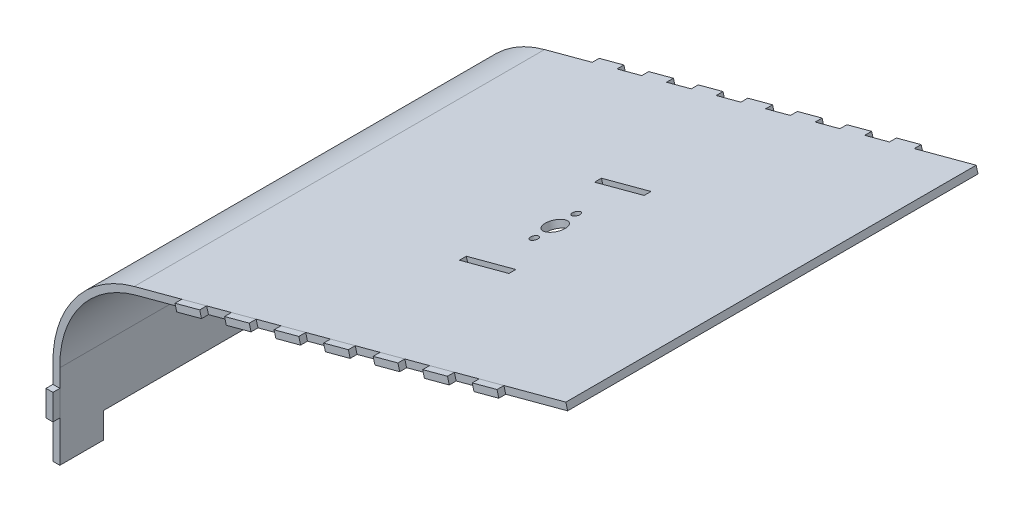
SolidWorks part; units mm, degrees
material "Maple"
ref_plane "Front Plane" through (0, 0, 0) normal (0, 0, 1) x (1, 0, 0)
ref_plane "Top Plane" through (0, 0, 0) normal (0, 1, 0) x (1, 0, 0)
ref_plane "Right Plane" through (0, 0, 0) normal (1, 0, 0) x (0, 0, -1)
sketch "Sketch1" plane through (0, 0, 0) normal (0, 0, 1) x (1, 0, 0)
  line L0 (-100, -27.0742) -> (-100, -60) construction
  line L1 (100, 60) -> (-68.3022, 14.9036) construction
  line L2 (-100, -27.0742) -> (-100, -60)
  line L3 (100, 60) -> (-68.3022, 14.9036)
  arc A0 (-68.3022, 14.9036) -> (-100, -27.0742) centre (-57.2316, -26.4125) ccw construction
  arc A1 (-68.3022, 14.9036) -> (-100, -27.0742) centre (-57.2316, -26.4125) ccw
extrude "Extrude-Thin1" add sketch "Sketch1" against normal blind 160 thin thin type one direction reverse wall 2.7
ref_plane "Plane1" through (0, 0, -80) normal (0, 0, 1) x (1, 0, 0)
sketch "Sketch2" plane through (0, 0, 0) normal (0, 0, 1) x (1, 0, 0)
  line L0 (100, -24) -> (97, -24) construction
  line L1 (97, -14) -> (97, -24) construction
  line L2 (100, -14) -> (97, -14) construction
  line L3 (75.8519, 53.5295) -> (76.6283, 50.6317) construction
  line L4 (-100, -44) -> (-97, -44)
  line L5 (-100, -34) -> (-100, -44)
  line L6 (-97, -34) -> (-100, -34)
  line L7 (-97, -44) -> (-97, -34)
  line L8 (-100, -60) -> (-80, -60)
  line L9 (-80, -60) -> (-80, -50)
  line L10 (-80, -50) -> (80, -50)
  line L11 (80, -50) -> (80, -60)
  line L12 (80, -60) -> (100, -60)
  line L13 (100, -60) -> (100, 60)
  line L14 (100, 60) -> (-68.3022, 14.9036)
  line L15 (-100, -27.0742) -> (-100, -60)
  line L16 (-100, -60) -> (-80, -60)
  line L17 (-80, -60) -> (-80, -50)
  line L18 (-80, -50) -> (80, -50)
  line L19 (80, -50) -> (80, -60)
  line L20 (80, -60) -> (100, -60)
  line L21 (100, -60) -> (100, 60)
  line L22 (100, 60) -> (-68.3022, 14.9036)
  line L23 (-100, -27.0742) -> (-100, -60)
  line L24 (-100, -44) -> (-97, -44)
  line L25 (-100, -34) -> (-100, -44)
  line L26 (-97, -34) -> (-100, -34)
  line L27 (-97, -44) -> (-97, -34)
  line L28 (100, -34) -> (97, -34)
  line L29 (100, -44) -> (100, -34)
  line L30 (97, -44) -> (100, -44)
  line L31 (97, -34) -> (97, -44)
  line L32 (100, -34) -> (97, -34)
  line L33 (100, -44) -> (100, -34)
  line L34 (97, -44) -> (100, -44)
  line L35 (97, -34) -> (97, -44)
  line L36 (-27, -44) -> (-27, -47)
  line L37 (-27, -47) -> (-17, -47)
  line L38 (-17, -47) -> (-17, -44)
  line L39 (-17, -44) -> (-27, -44)
  line L40 (-27, -44) -> (-27, -47)
  line L41 (-27, -47) -> (-17, -47)
  line L42 (-17, -47) -> (-17, -44)
  line L43 (-17, -44) -> (-27, -44)
  line L44 (-47, -44) -> (-47, -47)
  line L45 (-47, -47) -> (-37, -47)
  line L46 (-37, -47) -> (-37, -44)
  line L47 (-37, -44) -> (-47, -44)
  line L48 (-47, -44) -> (-47, -47)
  line L49 (-47, -47) -> (-37, -47)
  line L50 (-37, -47) -> (-37, -44)
  line L51 (-37, -44) -> (-47, -44)
  line L52 (-77, -44) -> (-87, -44)
  line L53 (-87, -44) -> (-87, -47)
  line L54 (-87, -47) -> (-77, -47)
  line L55 (-77, -47) -> (-77, -44)
  line L56 (-77, -44) -> (-87, -44)
  line L57 (-87, -44) -> (-87, -47)
  line L58 (-87, -47) -> (-77, -47)
  line L59 (-77, -47) -> (-77, -44)
  line L60 (-67, -44) -> (-67, -47)
  line L61 (-57, -44) -> (-67, -44)
  line L62 (-57, -47) -> (-57, -44)
  line L63 (-67, -47) -> (-57, -47)
  line L64 (-67, -44) -> (-67, -47)
  line L65 (-57, -44) -> (-67, -44)
  line L66 (-57, -47) -> (-57, -44)
  line L67 (-67, -47) -> (-57, -47)
  line L68 (53, -44) -> (53, -47)
  line L69 (53, -47) -> (63, -47)
  line L70 (63, -47) -> (63, -44)
  line L71 (63, -44) -> (53, -44)
  line L72 (53, -44) -> (53, -47)
  line L73 (53, -47) -> (63, -47)
  line L74 (63, -47) -> (63, -44)
  line L75 (63, -44) -> (53, -44)
  line L76 (33, -44) -> (33, -47)
  line L77 (33, -47) -> (43, -47)
  line L78 (43, -47) -> (43, -44)
  line L79 (43, -44) -> (33, -44)
  line L80 (33, -44) -> (33, -47)
  line L81 (33, -47) -> (43, -47)
  line L82 (43, -47) -> (43, -44)
  line L83 (43, -44) -> (33, -44)
  line L84 (13, -44) -> (13, -47)
  line L85 (13, -47) -> (23, -47)
  line L86 (23, -47) -> (23, -44)
  line L87 (23, -44) -> (13, -44)
  line L88 (13, -44) -> (13, -47)
  line L89 (13, -47) -> (23, -47)
  line L90 (23, -47) -> (23, -44)
  line L91 (23, -44) -> (13, -44)
  line L92 (-7, -44) -> (-7, -47)
  line L93 (3, -44) -> (-7, -44)
  line L94 (3, -47) -> (3, -44)
  line L95 (-7, -47) -> (3, -47)
  line L96 (-7, -44) -> (-7, -47)
  line L97 (3, -44) -> (-7, -44)
  line L98 (3, -47) -> (3, -44)
  line L99 (-7, -47) -> (3, -47)
  line L100 (73, -44) -> (73, -47)
  line L101 (83, -44) -> (73, -44)
  line L102 (83, -47) -> (83, -44)
  line L103 (73, -47) -> (83, -47)
  line L104 (73, -44) -> (73, -47)
  line L105 (83, -44) -> (73, -44)
  line L106 (83, -47) -> (83, -44)
  line L107 (73, -47) -> (83, -47)
  line L108 (76.6283, 50.6317) -> (66.9691, 48.0436) construction
  line L109 (66.9691, 48.0436) -> (66.1926, 50.9413) construction
  line L110 (56.5333, 48.3531) -> (57.3098, 45.4554) construction
  line L111 (57.3098, 45.4554) -> (47.6505, 42.8672) construction
  line L112 (47.6505, 42.8672) -> (46.8741, 45.765) construction
  line L113 (100, 36) -> (97, 36) construction
  line L114 (97, 46) -> (97, 36) construction
  line L115 (100, 46) -> (97, 46) construction
  line L116 (100, 16) -> (97, 16) construction
  line L117 (97, 26) -> (97, 16) construction
  line L118 (100, 26) -> (97, 26) construction
  line L119 (100, -4) -> (97, -4) construction
  line L120 (97, 6) -> (97, -4) construction
  line L121 (100, 6) -> (97, 6) construction
  line L122 (-20.7407, 27.6476) -> (-19.9643, 24.7498) construction
  line L123 (-19.9643, 24.7498) -> (-29.6235, 22.1617) construction
  line L124 (-29.6235, 22.1617) -> (-30.4, 25.0594) construction
  line L125 (-1.4222, 32.824) -> (-0.6458, 29.9262) construction
  line L126 (-0.6458, 29.9262) -> (-10.305, 27.338) construction
  line L127 (-10.305, 27.338) -> (-11.0815, 30.2358) construction
  line L128 (17.8963, 38.0004) -> (18.6728, 35.1026) construction
  line L129 (18.6728, 35.1026) -> (9.0135, 32.5144) construction
  line L130 (9.0135, 32.5144) -> (8.237, 35.4122) construction
  line L131 (37.2148, 43.1768) -> (37.9913, 40.279) construction
  line L132 (37.9913, 40.279) -> (28.332, 37.6908) construction
  line L133 (28.332, 37.6908) -> (27.5556, 40.5886) construction
  line L134 (-40.0592, 22.4712) -> (-39.2828, 19.5735) construction
  line L135 (-39.2828, 19.5735) -> (-48.942, 16.9853) construction
  line L136 (-48.942, 16.9853) -> (-49.7185, 19.883) construction
  line L137 (100, -24) -> (97, -24)
  line L138 (97, -14) -> (97, -24)
  line L139 (100, -14) -> (97, -14)
  line L140 (75.8519, 53.5295) -> (76.6283, 50.6317)
  line L141 (76.6283, 50.6317) -> (66.9691, 48.0436)
  line L142 (66.9691, 48.0436) -> (66.1926, 50.9413)
  line L143 (56.5333, 48.3531) -> (57.3098, 45.4554)
  line L144 (57.3098, 45.4554) -> (47.6505, 42.8672)
  line L145 (47.6505, 42.8672) -> (46.8741, 45.765)
  line L146 (100, 36) -> (97, 36)
  line L147 (97, 46) -> (97, 36)
  line L148 (100, 46) -> (97, 46)
  line L149 (100, 16) -> (97, 16)
  line L150 (97, 26) -> (97, 16)
  line L151 (100, 26) -> (97, 26)
  line L152 (100, -4) -> (97, -4)
  line L153 (97, 6) -> (97, -4)
  line L154 (100, 6) -> (97, 6)
  line L155 (-20.7407, 27.6476) -> (-19.9643, 24.7498)
  line L156 (-19.9643, 24.7498) -> (-29.6235, 22.1617)
  line L157 (-29.6235, 22.1617) -> (-30.4, 25.0594)
  line L158 (-1.4222, 32.824) -> (-0.6458, 29.9262)
  line L159 (-0.6458, 29.9262) -> (-10.305, 27.338)
  line L160 (-10.305, 27.338) -> (-11.0815, 30.2358)
  line L161 (17.8963, 38.0004) -> (18.6728, 35.1026)
  line L162 (18.6728, 35.1026) -> (9.0135, 32.5144)
  line L163 (9.0135, 32.5144) -> (8.237, 35.4122)
  line L164 (37.2148, 43.1768) -> (37.9913, 40.279)
  line L165 (37.9913, 40.279) -> (28.332, 37.6908)
  line L166 (28.332, 37.6908) -> (27.5556, 40.5886)
  line L167 (-40.0592, 22.4712) -> (-39.2828, 19.5735)
  line L168 (-39.2828, 19.5735) -> (-48.942, 16.9853)
  line L169 (-48.942, 16.9853) -> (-49.7185, 19.883)
  arc A1 (-68.3022, 14.9036) -> (-100, -27.0742) centre (-57.2316, -26.4125) ccw
  arc A2 (-68.3022, 14.9036) -> (-100, -27.0742) centre (-57.2316, -26.4125) ccw
  line M56 (-97.3, -60) -> (-97.3, -27.053)
  line M58 (-67.6034, 12.2956) -> (100.6988, 57.392)
  dimension "D1" = 0
  dimension "D2" = 0
  dimension "D3" = 0
  dimension "D4" = 0
  dimension "D5" = 0
  dimension "D6" = 0
  dimension "D7" = 0
  dimension "D8" = 0
  dimension "D9" = 0
  dimension "D10" = 0
  dimension "D11" = 0
  dimension "D12" = 0
extrude "Boss-Extrude1" add sketch "Sketch2" along normal blind 2.7 separate body contours L26 L23 L24 M56 | L169 L167 L22 M58 | L157 L155 L22 M58 | L160 L158 L22 M58 | L163 L161 L22 M58 | L166 L164 L22 M58 | L145 L143 L22 M58 | L142 L140 L22 M58
mirror "Mirror1" about plane through (0, 0, -80) normal (0, 0, 1) of "Boss-Extrude1"
sketch "Sketch3" plane through (-7.6025, 28.3728, 0) normal (0.2588, -0.9659, 0) x (0.9659, 0.2588, 0)
  line L0 (112.1217, -80) -> (-62.1176, -80) construction
  line L1 (112.1217, -160) -> (112.1217, 0) construction
  line L2 (-62.1176, -160) -> (-62.1176, 0) construction
  line L3 (25.0021, 2.7) -> (25.0021, -162.7) construction
  line L4 (17.1217, -162.7) -> (27.1217, -162.7) construction
  line L5 (15.0021, -105) -> (15.0021, -107.7)
  line L10 (25.553, -45.7096) -> (45.553, -43.0096) construction
  line L11 (25.553, -43.0096) -> (45.553, -45.7096) construction
  line L12 (15.0021, -55) -> (35.0021, -55)
  line L13 (15.0021, -55) -> (15.0021, -52.3)
  line L14 (15.0021, -52.3) -> (35.0021, -52.3)
  line L15 (35.0021, -55) -> (35.0021, -52.3)
  line L16 (15.0021, -55) -> (35.0021, -52.3) construction
  line L17 (15.0021, -52.3) -> (35.0021, -55) construction
  line L18 (15.0021, -107.7) -> (35.0021, -107.7)
  line L19 (35.0021, -105) -> (35.0021, -107.7)
  line L20 (15.0021, -105) -> (35.0021, -105)
  circle A0 centre (25.0021, -80) radius 4
  circle A1 centre (25.0021, -71.8075) radius 1.5
  circle A2 centre (25.0021, -88.1925) radius 1.5
  point P11 (25.0021, -80)
  point P17 (25.0021, -53.65)
  point P22 (35.553, -44.3596)
  dimension "D1" = 3
  dimension "D2" = 3
  dimension "D4" = 8
  dimension "D3" = 8.1925
  dimension "D5" = 8.1925
  dimension "D6" = 20
  dimension "D7" = 2.7
  dimension "D8" = 2.7
  dimension "D9" = 20
  dimension "D10" = 25
extrude "Cut-Extrude1" cut sketch "Sketch3" against normal blind 3
sketch "Sketch4" plane through (-100, 0, 0) normal (-1, 0, 0) x (0, 0, 1)
  line L0 (-160, -60) -> (0, -60) construction
  line L1 (-143, -60) -> (-17, -60)
  line L2 (-143, -60) -> (-143, -50)
  line L3 (-143, -50) -> (-17, -50)
  line L4 (-17, -60) -> (-17, -50)
  line L5 (-143, -60) -> (-17, -50) construction
  line L6 (-143, -50) -> (-17, -60) construction
  line L7 (-160, -44) -> (-160, -60) construction
  point P4 (-80, -55)
  dimension "D1" = 10
  dimension "D2" = 126
  dimension "D3" = 80
extrude "Cut-Extrude2" cut sketch "Sketch4" against normal blind 3
sketch "Sketch5" plane through (-100, 0, 0) normal (-1, 0, 0) x (0, 0, 1)
  line L0 (-155, -26.0742) -> (-143, -26.0742)
  line L1 (-160, -27.0742) -> (0, -27.0742) construction
  line L2 (-160, -27.0742) -> (-160, 29.5758) construction
  line L3 (-160, 29.5758) -> (0, 29.5758) construction
  line L4 (0, -27.0742) -> (0, 29.5758) construction
  line L5 (-160, -27.0742) -> (0, 29.5758) construction
  line L6 (-160, 29.5758) -> (0, -27.0742) construction
  line L7 (-140, -26.0742) -> (-128, -26.0742)
  line L8 (-125, -26.0742) -> (-113, -26.0742)
  line L9 (-110, -26.0742) -> (-98, -26.0742)
  line L10 (-95, -26.0742) -> (-83, -26.0742)
  line L11 (-80, -26.0742) -> (-68, -26.0742)
  line L12 (-65, -26.0742) -> (-53, -26.0742)
  line L13 (-50, -26.0742) -> (-38, -26.0742)
  line L14 (-35, -26.0742) -> (-23, -26.0742)
  line L15 (-20, -26.0742) -> (-8, -26.0742)
  line L16 (-5, -26.0742) -> (0, -26.0742)
  line L17 (-160, -25.0742) -> (-148, -25.0742)
  line L18 (-145, -25.0742) -> (-133, -25.0742)
  line L19 (-130, -25.0742) -> (-118, -25.0742)
  line L20 (-115, -25.0742) -> (-103, -25.0742)
  line L21 (-100, -25.0742) -> (-88, -25.0742)
  line L22 (-85, -25.0742) -> (-73, -25.0742)
  line L23 (-70, -25.0742) -> (-58, -25.0742)
  line L24 (-55, -25.0742) -> (-43, -25.0742)
  line L25 (-40, -25.0742) -> (-28, -25.0742)
  line L26 (-25, -25.0742) -> (-13, -25.0742)
  line L27 (-10, -25.0742) -> (2, -25.0742)
  line L29 (-155, -24.0742) -> (-143, -24.0742)
  line L30 (-140, -24.0742) -> (-128, -24.0742)
  line L31 (-125, -24.0742) -> (-113, -24.0742)
  line L32 (-110, -24.0742) -> (-98, -24.0742)
  line L33 (-95, -24.0742) -> (-83, -24.0742)
  line L34 (-80, -24.0742) -> (-68, -24.0742)
  line L35 (-65, -24.0742) -> (-53, -24.0742)
  line L36 (-50, -24.0742) -> (-38, -24.0742)
  line L37 (-35, -24.0742) -> (-23, -24.0742)
  line L38 (-20, -24.0742) -> (-8, -24.0742)
  line L39 (-5, -24.0742) -> (0, -24.0742)
  line L40 (-160, -23.0742) -> (-148, -23.0742)
  line L41 (-145, -23.0742) -> (-133, -23.0742)
  line L42 (-130, -23.0742) -> (-118, -23.0742)
  line L43 (-115, -23.0742) -> (-103, -23.0742)
  line L44 (-100, -23.0742) -> (-88, -23.0742)
  line L45 (-85, -23.0742) -> (-73, -23.0742)
  line L46 (-70, -23.0742) -> (-58, -23.0742)
  line L47 (-55, -23.0742) -> (-43, -23.0742)
  line L48 (-40, -23.0742) -> (-28, -23.0742)
  line L49 (-25, -23.0742) -> (-13, -23.0742)
  line L50 (-10, -23.0742) -> (2, -23.0742)
  line L51 (-155, -22.0742) -> (-143, -22.0742)
  line L52 (-140, -22.0742) -> (-128, -22.0742)
  line L53 (-125, -22.0742) -> (-113, -22.0742)
  line L54 (-110, -22.0742) -> (-98, -22.0742)
  line L55 (-95, -22.0742) -> (-83, -22.0742)
  line L56 (-80, -22.0742) -> (-68, -22.0742)
  line L57 (-65, -22.0742) -> (-53, -22.0742)
  line L58 (-50, -22.0742) -> (-38, -22.0742)
  line L59 (-35, -22.0742) -> (-23, -22.0742)
  line L60 (-20, -22.0742) -> (-8, -22.0742)
  line L61 (-5, -22.0742) -> (0, -22.0742)
  line L62 (-160, -21.0742) -> (-148, -21.0742)
  line L63 (-145, -21.0742) -> (-133, -21.0742)
  line L64 (-130, -21.0742) -> (-118, -21.0742)
  line L65 (-115, -21.0742) -> (-103, -21.0742)
  line L66 (-100, -21.0742) -> (-88, -21.0742)
  line L67 (-85, -21.0742) -> (-73, -21.0742)
  line L68 (-70, -21.0742) -> (-58, -21.0742)
  line L69 (-55, -21.0742) -> (-43, -21.0742)
  line L70 (-40, -21.0742) -> (-28, -21.0742)
  line L71 (-25, -21.0742) -> (-13, -21.0742)
  line L72 (-10, -21.0742) -> (2, -21.0742)
  line L73 (-155, -20.0742) -> (-143, -20.0742)
  line L74 (-140, -20.0742) -> (-128, -20.0742)
  line L75 (-125, -20.0742) -> (-113, -20.0742)
  line L76 (-110, -20.0742) -> (-98, -20.0742)
  line L77 (-95, -20.0742) -> (-83, -20.0742)
  line L78 (-80, -20.0742) -> (-68, -20.0742)
  line L79 (-65, -20.0742) -> (-53, -20.0742)
  line L80 (-50, -20.0742) -> (-38, -20.0742)
  line L81 (-35, -20.0742) -> (-23, -20.0742)
  line L82 (-20, -20.0742) -> (-8, -20.0742)
  line L83 (-5, -20.0742) -> (0, -20.0742)
  line L84 (-160, -19.0742) -> (-148, -19.0742)
  line L85 (-145, -19.0742) -> (-133, -19.0742)
  line L86 (-130, -19.0742) -> (-118, -19.0742)
  line L87 (-115, -19.0742) -> (-103, -19.0742)
  line L88 (-100, -19.0742) -> (-88, -19.0742)
  line L89 (-85, -19.0742) -> (-73, -19.0742)
  line L90 (-70, -19.0742) -> (-58, -19.0742)
  line L91 (-55, -19.0742) -> (-43, -19.0742)
  line L92 (-40, -19.0742) -> (-28, -19.0742)
  line L93 (-25, -19.0742) -> (-13, -19.0742)
  line L94 (-10, -19.0742) -> (2, -19.0742)
  line L95 (-155, -18.0742) -> (-143, -18.0742)
  line L96 (-140, -18.0742) -> (-128, -18.0742)
  line L97 (-125, -18.0742) -> (-113, -18.0742)
  line L98 (-110, -18.0742) -> (-98, -18.0742)
  line L99 (-95, -18.0742) -> (-83, -18.0742)
  line L100 (-80, -18.0742) -> (-68, -18.0742)
  line L101 (-65, -18.0742) -> (-53, -18.0742)
  line L102 (-50, -18.0742) -> (-38, -18.0742)
  line L103 (-35, -18.0742) -> (-23, -18.0742)
  line L104 (-20, -18.0742) -> (-8, -18.0742)
  line L105 (-5, -18.0742) -> (0, -18.0742)
  line L106 (-160, -17.0742) -> (-148, -17.0742)
  line L107 (-145, -17.0742) -> (-133, -17.0742)
  line L108 (-130, -17.0742) -> (-118, -17.0742)
  line L109 (-115, -17.0742) -> (-103, -17.0742)
  line L110 (-100, -17.0742) -> (-88, -17.0742)
  line L111 (-85, -17.0742) -> (-73, -17.0742)
  line L112 (-70, -17.0742) -> (-58, -17.0742)
  line L113 (-55, -17.0742) -> (-43, -17.0742)
  line L114 (-40, -17.0742) -> (-28, -17.0742)
  line L115 (-25, -17.0742) -> (-13, -17.0742)
  line L116 (-10, -17.0742) -> (2, -17.0742)
  line L117 (-155, -16.0742) -> (-143, -16.0742)
  line L118 (-140, -16.0742) -> (-128, -16.0742)
  line L119 (-125, -16.0742) -> (-113, -16.0742)
  line L120 (-110, -16.0742) -> (-98, -16.0742)
  line L121 (-95, -16.0742) -> (-83, -16.0742)
  line L122 (-80, -16.0742) -> (-68, -16.0742)
  line L123 (-65, -16.0742) -> (-53, -16.0742)
  line L124 (-50, -16.0742) -> (-38, -16.0742)
  line L125 (-35, -16.0742) -> (-23, -16.0742)
  line L126 (-20, -16.0742) -> (-8, -16.0742)
  line L127 (-5, -16.0742) -> (0, -16.0742)
  line L128 (-160, -15.0742) -> (-148, -15.0742)
  line L129 (-145, -15.0742) -> (-133, -15.0742)
  line L130 (-130, -15.0742) -> (-118, -15.0742)
  line L131 (-115, -15.0742) -> (-103, -15.0742)
  line L132 (-100, -15.0742) -> (-88, -15.0742)
  line L133 (-85, -15.0742) -> (-73, -15.0742)
  line L134 (-70, -15.0742) -> (-58, -15.0742)
  line L135 (-55, -15.0742) -> (-43, -15.0742)
  line L136 (-40, -15.0742) -> (-28, -15.0742)
  line L137 (-25, -15.0742) -> (-13, -15.0742)
  line L138 (-10, -15.0742) -> (2, -15.0742)
  line L139 (-155, -14.0742) -> (-143, -14.0742)
  line L140 (-140, -14.0742) -> (-128, -14.0742)
  line L141 (-125, -14.0742) -> (-113, -14.0742)
  line L142 (-110, -14.0742) -> (-98, -14.0742)
  line L143 (-95, -14.0742) -> (-83, -14.0742)
  line L144 (-80, -14.0742) -> (-68, -14.0742)
  line L145 (-65, -14.0742) -> (-53, -14.0742)
  line L146 (-50, -14.0742) -> (-38, -14.0742)
  line L147 (-35, -14.0742) -> (-23, -14.0742)
  line L148 (-20, -14.0742) -> (-8, -14.0742)
  line L149 (-5, -14.0742) -> (0, -14.0742)
  line L150 (-160, -13.0742) -> (-148, -13.0742)
  line L151 (-145, -13.0742) -> (-133, -13.0742)
  line L152 (-130, -13.0742) -> (-118, -13.0742)
  line L153 (-115, -13.0742) -> (-103, -13.0742)
  line L154 (-100, -13.0742) -> (-88, -13.0742)
  line L155 (-85, -13.0742) -> (-73, -13.0742)
  line L156 (-70, -13.0742) -> (-58, -13.0742)
  line L157 (-55, -13.0742) -> (-43, -13.0742)
  line L158 (-40, -13.0742) -> (-28, -13.0742)
  line L159 (-25, -13.0742) -> (-13, -13.0742)
  line L160 (-10, -13.0742) -> (2, -13.0742)
  line L161 (-155, -12.0742) -> (-143, -12.0742)
  line L162 (-140, -12.0742) -> (-128, -12.0742)
  line L163 (-125, -12.0742) -> (-113, -12.0742)
  line L164 (-110, -12.0742) -> (-98, -12.0742)
  line L165 (-95, -12.0742) -> (-83, -12.0742)
  line L166 (-80, -12.0742) -> (-68, -12.0742)
  line L167 (-65, -12.0742) -> (-53, -12.0742)
  line L168 (-50, -12.0742) -> (-38, -12.0742)
  line L169 (-35, -12.0742) -> (-23, -12.0742)
  line L170 (-20, -12.0742) -> (-8, -12.0742)
  line L171 (-5, -12.0742) -> (0, -12.0742)
  line L172 (-160, -11.0742) -> (-148, -11.0742)
  line L173 (-145, -11.0742) -> (-133, -11.0742)
  line L174 (-130, -11.0742) -> (-118, -11.0742)
  line L175 (-115, -11.0742) -> (-103, -11.0742)
  line L176 (-100, -11.0742) -> (-88, -11.0742)
  line L177 (-85, -11.0742) -> (-73, -11.0742)
  line L178 (-70, -11.0742) -> (-58, -11.0742)
  line L179 (-55, -11.0742) -> (-43, -11.0742)
  line L180 (-40, -11.0742) -> (-28, -11.0742)
  line L181 (-25, -11.0742) -> (-13, -11.0742)
  line L182 (-10, -11.0742) -> (2, -11.0742)
  line L183 (-155, -10.0742) -> (-143, -10.0742)
  line L184 (-140, -10.0742) -> (-128, -10.0742)
  line L185 (-125, -10.0742) -> (-113, -10.0742)
  line L186 (-110, -10.0742) -> (-98, -10.0742)
  line L187 (-95, -10.0742) -> (-83, -10.0742)
  line L188 (-80, -10.0742) -> (-68, -10.0742)
  line L189 (-65, -10.0742) -> (-53, -10.0742)
  line L190 (-50, -10.0742) -> (-38, -10.0742)
  line L191 (-35, -10.0742) -> (-23, -10.0742)
  line L192 (-20, -10.0742) -> (-8, -10.0742)
  line L193 (-5, -10.0742) -> (0, -10.0742)
  line L194 (-160, -9.0742) -> (-148, -9.0742)
  line L195 (-145, -9.0742) -> (-133, -9.0742)
  line L196 (-130, -9.0742) -> (-118, -9.0742)
  line L197 (-115, -9.0742) -> (-103, -9.0742)
  line L198 (-100, -9.0742) -> (-88, -9.0742)
  line L199 (-85, -9.0742) -> (-73, -9.0742)
  line L200 (-70, -9.0742) -> (-58, -9.0742)
  line L201 (-55, -9.0742) -> (-43, -9.0742)
  line L202 (-40, -9.0742) -> (-28, -9.0742)
  line L203 (-25, -9.0742) -> (-13, -9.0742)
  line L204 (-10, -9.0742) -> (2, -9.0742)
  line L205 (-155, -8.0742) -> (-143, -8.0742)
  line L206 (-140, -8.0742) -> (-128, -8.0742)
  line L207 (-125, -8.0742) -> (-113, -8.0742)
  line L208 (-110, -8.0742) -> (-98, -8.0742)
  line L209 (-95, -8.0742) -> (-83, -8.0742)
  line L210 (-80, -8.0742) -> (-68, -8.0742)
  line L211 (-65, -8.0742) -> (-53, -8.0742)
  line L212 (-50, -8.0742) -> (-38, -8.0742)
  line L213 (-35, -8.0742) -> (-23, -8.0742)
  line L214 (-20, -8.0742) -> (-8, -8.0742)
  line L215 (-5, -8.0742) -> (0, -8.0742)
  line L216 (-160, -7.0742) -> (-148, -7.0742)
  line L217 (-145, -7.0742) -> (-133, -7.0742)
  line L218 (-130, -7.0742) -> (-118, -7.0742)
  line L219 (-115, -7.0742) -> (-103, -7.0742)
  line L220 (-100, -7.0742) -> (-88, -7.0742)
  line L221 (-85, -7.0742) -> (-73, -7.0742)
  line L222 (-70, -7.0742) -> (-58, -7.0742)
  line L223 (-55, -7.0742) -> (-43, -7.0742)
  line L224 (-40, -7.0742) -> (-28, -7.0742)
  line L225 (-25, -7.0742) -> (-13, -7.0742)
  line L226 (-10, -7.0742) -> (2, -7.0742)
  line L227 (-155, -6.0742) -> (-143, -6.0742)
  line L228 (-140, -6.0742) -> (-128, -6.0742)
  line L229 (-125, -6.0742) -> (-113, -6.0742)
  line L230 (-110, -6.0742) -> (-98, -6.0742)
  line L231 (-95, -6.0742) -> (-83, -6.0742)
  line L232 (-80, -6.0742) -> (-68, -6.0742)
  line L233 (-65, -6.0742) -> (-53, -6.0742)
  line L234 (-50, -6.0742) -> (-38, -6.0742)
  line L235 (-35, -6.0742) -> (-23, -6.0742)
  line L236 (-20, -6.0742) -> (-8, -6.0742)
  line L237 (-5, -6.0742) -> (0, -6.0742)
  line L238 (-160, -5.0742) -> (-148, -5.0742)
  line L239 (-145, -5.0742) -> (-133, -5.0742)
  line L240 (-130, -5.0742) -> (-118, -5.0742)
  line L241 (-115, -5.0742) -> (-103, -5.0742)
  line L242 (-100, -5.0742) -> (-88, -5.0742)
  line L243 (-85, -5.0742) -> (-73, -5.0742)
  line L244 (-70, -5.0742) -> (-58, -5.0742)
  line L245 (-55, -5.0742) -> (-43, -5.0742)
  line L246 (-40, -5.0742) -> (-28, -5.0742)
  line L247 (-25, -5.0742) -> (-13, -5.0742)
  line L248 (-10, -5.0742) -> (2, -5.0742)
  line L249 (-155, -4.0742) -> (-143, -4.0742)
  line L250 (-140, -4.0742) -> (-128, -4.0742)
  line L251 (-125, -4.0742) -> (-113, -4.0742)
  line L252 (-110, -4.0742) -> (-98, -4.0742)
  line L253 (-95, -4.0742) -> (-83, -4.0742)
  line L254 (-80, -4.0742) -> (-68, -4.0742)
  line L255 (-65, -4.0742) -> (-53, -4.0742)
  line L256 (-50, -4.0742) -> (-38, -4.0742)
  line L257 (-35, -4.0742) -> (-23, -4.0742)
  line L258 (-20, -4.0742) -> (-8, -4.0742)
  line L259 (-5, -4.0742) -> (0, -4.0742)
  line L260 (-160, -3.0742) -> (-148, -3.0742)
  line L261 (-145, -3.0742) -> (-133, -3.0742)
  line L262 (-130, -3.0742) -> (-118, -3.0742)
  line L263 (-115, -3.0742) -> (-103, -3.0742)
  line L264 (-100, -3.0742) -> (-88, -3.0742)
  line L265 (-85, -3.0742) -> (-73, -3.0742)
  line L266 (-70, -3.0742) -> (-58, -3.0742)
  line L267 (-55, -3.0742) -> (-43, -3.0742)
  line L268 (-40, -3.0742) -> (-28, -3.0742)
  line L269 (-25, -3.0742) -> (-13, -3.0742)
  line L270 (-10, -3.0742) -> (2, -3.0742)
  line L271 (-155, -2.0742) -> (-143, -2.0742)
  line L272 (-140, -2.0742) -> (-128, -2.0742)
  line L273 (-125, -2.0742) -> (-113, -2.0742)
  line L274 (-110, -2.0742) -> (-98, -2.0742)
  line L275 (-95, -2.0742) -> (-83, -2.0742)
  line L276 (-80, -2.0742) -> (-68, -2.0742)
  line L277 (-65, -2.0742) -> (-53, -2.0742)
  line L278 (-50, -2.0742) -> (-38, -2.0742)
  line L279 (-35, -2.0742) -> (-23, -2.0742)
  line L280 (-20, -2.0742) -> (-8, -2.0742)
  line L281 (-5, -2.0742) -> (0, -2.0742)
  line L282 (-160, -1.0742) -> (-148, -1.0742)
  line L283 (-145, -1.0742) -> (-133, -1.0742)
  line L284 (-130, -1.0742) -> (-118, -1.0742)
  line L285 (-115, -1.0742) -> (-103, -1.0742)
  line L286 (-100, -1.0742) -> (-88, -1.0742)
  line L287 (-85, -1.0742) -> (-73, -1.0742)
  line L288 (-70, -1.0742) -> (-58, -1.0742)
  line L289 (-55, -1.0742) -> (-43, -1.0742)
  line L290 (-40, -1.0742) -> (-28, -1.0742)
  line L291 (-25, -1.0742) -> (-13, -1.0742)
  line L292 (-10, -1.0742) -> (2, -1.0742)
  line L293 (-155, -0.0742) -> (-143, -0.0742)
  line L294 (-140, -0.0742) -> (-128, -0.0742)
  line L295 (-125, -0.0742) -> (-113, -0.0742)
  line L296 (-110, -0.0742) -> (-98, -0.0742)
  line L297 (-95, -0.0742) -> (-83, -0.0742)
  line L298 (-80, -0.0742) -> (-68, -0.0742)
  line L299 (-65, -0.0742) -> (-53, -0.0742)
  line L300 (-50, -0.0742) -> (-38, -0.0742)
  line L301 (-35, -0.0742) -> (-23, -0.0742)
  line L302 (-20, -0.0742) -> (-8, -0.0742)
  line L303 (-5, -0.0742) -> (0, -0.0742)
  line L304 (-160, 0.9258) -> (-148, 0.9258)
  line L305 (-145, 0.9258) -> (-133, 0.9258)
  line L306 (-130, 0.9258) -> (-118, 0.9258)
  line L307 (-115, 0.9258) -> (-103, 0.9258)
  line L308 (-100, 0.9258) -> (-88, 0.9258)
  line L309 (-85, 0.9258) -> (-73, 0.9258)
  line L310 (-70, 0.9258) -> (-58, 0.9258)
  line L311 (-55, 0.9258) -> (-43, 0.9258)
  line L312 (-40, 0.9258) -> (-28, 0.9258)
  line L313 (-25, 0.9258) -> (-13, 0.9258)
  line L314 (-10, 0.9258) -> (2, 0.9258)
  line L315 (-10, 2.9258) -> (2, 2.9258)
  line L316 (-5, 1.9258) -> (0, 1.9258)
  line L317 (-20, 1.9258) -> (-8, 1.9258)
  line L318 (-25, 2.9258) -> (-13, 2.9258)
  line L319 (-35, 1.9258) -> (-23, 1.9258)
  line L320 (-40, 2.9258) -> (-28, 2.9258)
  line L321 (-50, 1.9258) -> (-38, 1.9258)
  line L322 (-55, 2.9258) -> (-43, 2.9258)
  line L323 (-65, 1.9258) -> (-53, 1.9258)
  line L324 (-70, 2.9258) -> (-58, 2.9258)
  line L325 (-80, 1.9258) -> (-68, 1.9258)
  line L326 (-85, 2.9258) -> (-73, 2.9258)
  line L327 (-95, 1.9258) -> (-83, 1.9258)
  line L328 (-100, 2.9258) -> (-88, 2.9258)
  line L329 (-110, 1.9258) -> (-98, 1.9258)
  line L330 (-115, 2.9258) -> (-103, 2.9258)
  line L331 (-125, 1.9258) -> (-113, 1.9258)
  line L332 (-130, 2.9258) -> (-118, 2.9258)
  line L333 (-140, 1.9258) -> (-128, 1.9258)
  line L334 (-145, 2.9258) -> (-133, 2.9258)
  line L335 (-155, 1.9258) -> (-143, 1.9258)
  line L336 (-160, 2.9258) -> (-148, 2.9258)
  line L337 (-10, 4.9258) -> (2, 4.9258)
  line L338 (-5, 3.9258) -> (0, 3.9258)
  line L339 (-20, 3.9258) -> (-8, 3.9258)
  line L340 (-25, 4.9258) -> (-13, 4.9258)
  line L341 (-35, 3.9258) -> (-23, 3.9258)
  line L342 (-40, 4.9258) -> (-28, 4.9258)
  line L343 (-50, 3.9258) -> (-38, 3.9258)
  line L344 (-55, 4.9258) -> (-43, 4.9258)
  line L345 (-65, 3.9258) -> (-53, 3.9258)
  line L346 (-70, 4.9258) -> (-58, 4.9258)
  line L347 (-80, 3.9258) -> (-68, 3.9258)
  line L348 (-85, 4.9258) -> (-73, 4.9258)
  line L349 (-95, 3.9258) -> (-83, 3.9258)
  line L350 (-100, 4.9258) -> (-88, 4.9258)
  line L351 (-110, 3.9258) -> (-98, 3.9258)
  line L352 (-115, 4.9258) -> (-103, 4.9258)
  line L353 (-125, 3.9258) -> (-113, 3.9258)
  line L354 (-130, 4.9258) -> (-118, 4.9258)
  line L355 (-140, 3.9258) -> (-128, 3.9258)
  line L356 (-145, 4.9258) -> (-133, 4.9258)
  line L357 (-155, 3.9258) -> (-143, 3.9258)
  line L358 (-160, 4.9258) -> (-148, 4.9258)
  line L359 (-10, 6.9258) -> (2, 6.9258)
  line L360 (-5, 5.9258) -> (0, 5.9258)
  line L361 (-20, 5.9258) -> (-8, 5.9258)
  line L362 (-25, 6.9258) -> (-13, 6.9258)
  line L363 (-35, 5.9258) -> (-23, 5.9258)
  line L364 (-40, 6.9258) -> (-28, 6.9258)
  line L365 (-50, 5.9258) -> (-38, 5.9258)
  line L366 (-55, 6.9258) -> (-43, 6.9258)
  line L367 (-65, 5.9258) -> (-53, 5.9258)
  line L368 (-70, 6.9258) -> (-58, 6.9258)
  line L369 (-80, 5.9258) -> (-68, 5.9258)
  line L370 (-85, 6.9258) -> (-73, 6.9258)
  line L371 (-95, 5.9258) -> (-83, 5.9258)
  line L372 (-100, 6.9258) -> (-88, 6.9258)
  line L373 (-110, 5.9258) -> (-98, 5.9258)
  line L374 (-115, 6.9258) -> (-103, 6.9258)
  line L375 (-125, 5.9258) -> (-113, 5.9258)
  line L376 (-130, 6.9258) -> (-118, 6.9258)
  line L377 (-140, 5.9258) -> (-128, 5.9258)
  line L378 (-145, 6.9258) -> (-133, 6.9258)
  line L379 (-155, 5.9258) -> (-143, 5.9258)
  line L380 (-160, 6.9258) -> (-148, 6.9258)
  line L381 (-10, 8.9258) -> (2, 8.9258)
  line L382 (-5, 7.9258) -> (0, 7.9258)
  line L383 (-20, 7.9258) -> (-8, 7.9258)
  line L384 (-25, 8.9258) -> (-13, 8.9258)
  line L385 (-35, 7.9258) -> (-23, 7.9258)
  line L386 (-40, 8.9258) -> (-28, 8.9258)
  line L387 (-50, 7.9258) -> (-38, 7.9258)
  line L388 (-55, 8.9258) -> (-43, 8.9258)
  line L389 (-65, 7.9258) -> (-53, 7.9258)
  line L390 (-70, 8.9258) -> (-58, 8.9258)
  line L391 (-80, 7.9258) -> (-68, 7.9258)
  line L392 (-85, 8.9258) -> (-73, 8.9258)
  line L393 (-95, 7.9258) -> (-83, 7.9258)
  line L394 (-100, 8.9258) -> (-88, 8.9258)
  line L395 (-110, 7.9258) -> (-98, 7.9258)
  line L396 (-115, 8.9258) -> (-103, 8.9258)
  line L397 (-125, 7.9258) -> (-113, 7.9258)
  line L398 (-130, 8.9258) -> (-118, 8.9258)
  line L399 (-140, 7.9258) -> (-128, 7.9258)
  line L400 (-145, 8.9258) -> (-133, 8.9258)
  line L401 (-155, 7.9258) -> (-143, 7.9258)
  line L402 (-160, 8.9258) -> (-148, 8.9258)
  line L403 (-10, 10.9258) -> (2, 10.9258)
  line L404 (-5, 9.9258) -> (0, 9.9258)
  line L405 (-20, 9.9258) -> (-8, 9.9258)
  line L406 (-25, 10.9258) -> (-13, 10.9258)
  line L407 (-35, 9.9258) -> (-23, 9.9258)
  line L408 (-40, 10.9258) -> (-28, 10.9258)
  line L409 (-50, 9.9258) -> (-38, 9.9258)
  line L410 (-55, 10.9258) -> (-43, 10.9258)
  line L411 (-65, 9.9258) -> (-53, 9.9258)
  line L412 (-70, 10.9258) -> (-58, 10.9258)
  line L413 (-80, 9.9258) -> (-68, 9.9258)
  line L414 (-85, 10.9258) -> (-73, 10.9258)
  line L415 (-95, 9.9258) -> (-83, 9.9258)
  line L416 (-100, 10.9258) -> (-88, 10.9258)
  line L417 (-110, 9.9258) -> (-98, 9.9258)
  line L418 (-115, 10.9258) -> (-103, 10.9258)
  line L419 (-125, 9.9258) -> (-113, 9.9258)
  line L420 (-130, 10.9258) -> (-118, 10.9258)
  line L421 (-140, 9.9258) -> (-128, 9.9258)
  line L422 (-145, 10.9258) -> (-133, 10.9258)
  line L423 (-155, 9.9258) -> (-143, 9.9258)
  line L424 (-160, 10.9258) -> (-148, 10.9258)
  line L425 (-10, 12.9258) -> (2, 12.9258)
  line L426 (-5, 11.9258) -> (0, 11.9258)
  line L427 (-20, 11.9258) -> (-8, 11.9258)
  line L428 (-25, 12.9258) -> (-13, 12.9258)
  line L429 (-35, 11.9258) -> (-23, 11.9258)
  line L430 (-40, 12.9258) -> (-28, 12.9258)
  line L431 (-50, 11.9258) -> (-38, 11.9258)
  line L432 (-55, 12.9258) -> (-43, 12.9258)
  line L433 (-65, 11.9258) -> (-53, 11.9258)
  line L434 (-70, 12.9258) -> (-58, 12.9258)
  line L435 (-80, 11.9258) -> (-68, 11.9258)
  line L436 (-85, 12.9258) -> (-73, 12.9258)
  line L437 (-95, 11.9258) -> (-83, 11.9258)
  line L438 (-100, 12.9258) -> (-88, 12.9258)
  line L439 (-110, 11.9258) -> (-98, 11.9258)
  line L440 (-115, 12.9258) -> (-103, 12.9258)
  line L441 (-125, 11.9258) -> (-113, 11.9258)
  line L442 (-130, 12.9258) -> (-118, 12.9258)
  line L443 (-140, 11.9258) -> (-128, 11.9258)
  line L444 (-145, 12.9258) -> (-133, 12.9258)
  line L445 (-155, 11.9258) -> (-143, 11.9258)
  line L446 (-160, 12.9258) -> (-148, 12.9258)
  line L447 (-10, 14.9258) -> (2, 14.9258)
  line L448 (-5, 13.9258) -> (0, 13.9258)
  line L449 (-20, 13.9258) -> (-8, 13.9258)
  line L450 (-25, 14.9258) -> (-13, 14.9258)
  line L451 (-35, 13.9258) -> (-23, 13.9258)
  line L452 (-40, 14.9258) -> (-28, 14.9258)
  line L453 (-50, 13.9258) -> (-38, 13.9258)
  line L454 (-55, 14.9258) -> (-43, 14.9258)
  line L455 (-65, 13.9258) -> (-53, 13.9258)
  line L456 (-70, 14.9258) -> (-58, 14.9258)
  line L457 (-80, 13.9258) -> (-68, 13.9258)
  line L458 (-85, 14.9258) -> (-73, 14.9258)
  line L459 (-95, 13.9258) -> (-83, 13.9258)
  line L460 (-100, 14.9258) -> (-88, 14.9258)
  line L461 (-110, 13.9258) -> (-98, 13.9258)
  line L462 (-115, 14.9258) -> (-103, 14.9258)
  line L463 (-125, 13.9258) -> (-113, 13.9258)
  line L464 (-130, 14.9258) -> (-118, 14.9258)
  line L465 (-140, 13.9258) -> (-128, 13.9258)
  line L466 (-145, 14.9258) -> (-133, 14.9258)
  line L467 (-155, 13.9258) -> (-143, 13.9258)
  line L468 (-160, 14.9258) -> (-148, 14.9258)
  line L469 (-10, 16.9258) -> (2, 16.9258)
  line L470 (-5, 15.9258) -> (0, 15.9258)
  line L471 (-20, 15.9258) -> (-8, 15.9258)
  line L472 (-25, 16.9258) -> (-13, 16.9258)
  line L473 (-35, 15.9258) -> (-23, 15.9258)
  line L474 (-40, 16.9258) -> (-28, 16.9258)
  line L475 (-50, 15.9258) -> (-38, 15.9258)
  line L476 (-55, 16.9258) -> (-43, 16.9258)
  line L477 (-65, 15.9258) -> (-53, 15.9258)
  line L478 (-70, 16.9258) -> (-58, 16.9258)
  line L479 (-80, 15.9258) -> (-68, 15.9258)
  line L480 (-85, 16.9258) -> (-73, 16.9258)
  line L481 (-95, 15.9258) -> (-83, 15.9258)
  line L482 (-100, 16.9258) -> (-88, 16.9258)
  line L483 (-110, 15.9258) -> (-98, 15.9258)
  line L484 (-115, 16.9258) -> (-103, 16.9258)
  line L485 (-125, 15.9258) -> (-113, 15.9258)
  line L486 (-130, 16.9258) -> (-118, 16.9258)
  line L487 (-140, 15.9258) -> (-128, 15.9258)
  line L488 (-145, 16.9258) -> (-133, 16.9258)
  line L489 (-155, 15.9258) -> (-143, 15.9258)
  line L490 (-160, 16.9258) -> (-148, 16.9258)
  line L491 (-10, 18.9258) -> (2, 18.9258)
  line L492 (-5, 17.9258) -> (0, 17.9258)
  line L493 (-20, 17.9258) -> (-8, 17.9258)
  line L494 (-25, 18.9258) -> (-13, 18.9258)
  line L495 (-35, 17.9258) -> (-23, 17.9258)
  line L496 (-40, 18.9258) -> (-28, 18.9258)
  line L497 (-50, 17.9258) -> (-38, 17.9258)
  line L498 (-55, 18.9258) -> (-43, 18.9258)
  line L499 (-65, 17.9258) -> (-53, 17.9258)
  line L500 (-70, 18.9258) -> (-58, 18.9258)
  line L501 (-80, 17.9258) -> (-68, 17.9258)
  line L502 (-85, 18.9258) -> (-73, 18.9258)
  line L503 (-95, 17.9258) -> (-83, 17.9258)
  line L504 (-100, 18.9258) -> (-88, 18.9258)
  line L505 (-110, 17.9258) -> (-98, 17.9258)
  line L506 (-115, 18.9258) -> (-103, 18.9258)
  line L507 (-125, 17.9258) -> (-113, 17.9258)
  line L508 (-130, 18.9258) -> (-118, 18.9258)
  line L509 (-140, 17.9258) -> (-128, 17.9258)
  line L510 (-145, 18.9258) -> (-133, 18.9258)
  line L511 (-155, 17.9258) -> (-143, 17.9258)
  line L512 (-160, 18.9258) -> (-148, 18.9258)
  line L513 (-10, 20.9258) -> (2, 20.9258)
  line L514 (-5, 19.9258) -> (0, 19.9258)
  line L515 (-20, 19.9258) -> (-8, 19.9258)
  line L516 (-25, 20.9258) -> (-13, 20.9258)
  line L517 (-35, 19.9258) -> (-23, 19.9258)
  line L518 (-40, 20.9258) -> (-28, 20.9258)
  line L519 (-50, 19.9258) -> (-38, 19.9258)
  line L520 (-55, 20.9258) -> (-43, 20.9258)
  line L521 (-65, 19.9258) -> (-53, 19.9258)
  line L522 (-70, 20.9258) -> (-58, 20.9258)
  line L523 (-80, 19.9258) -> (-68, 19.9258)
  line L524 (-85, 20.9258) -> (-73, 20.9258)
  line L525 (-95, 19.9258) -> (-83, 19.9258)
  line L526 (-100, 20.9258) -> (-88, 20.9258)
  line L527 (-110, 19.9258) -> (-98, 19.9258)
  line L528 (-115, 20.9258) -> (-103, 20.9258)
  line L529 (-125, 19.9258) -> (-113, 19.9258)
  line L530 (-130, 20.9258) -> (-118, 20.9258)
  line L531 (-140, 19.9258) -> (-128, 19.9258)
  line L532 (-145, 20.9258) -> (-133, 20.9258)
  line L533 (-155, 19.9258) -> (-143, 19.9258)
  line L534 (-160, 20.9258) -> (-148, 20.9258)
  line L535 (-10, 22.9258) -> (2, 22.9258)
  line L536 (-5, 21.9258) -> (0, 21.9258)
  line L537 (-20, 21.9258) -> (-8, 21.9258)
  line L538 (-25, 22.9258) -> (-13, 22.9258)
  line L539 (-35, 21.9258) -> (-23, 21.9258)
  line L540 (-40, 22.9258) -> (-28, 22.9258)
  line L541 (-50, 21.9258) -> (-38, 21.9258)
  line L542 (-55, 22.9258) -> (-43, 22.9258)
  line L543 (-65, 21.9258) -> (-53, 21.9258)
  line L544 (-70, 22.9258) -> (-58, 22.9258)
  line L545 (-80, 21.9258) -> (-68, 21.9258)
  line L546 (-85, 22.9258) -> (-73, 22.9258)
  line L547 (-95, 21.9258) -> (-83, 21.9258)
  line L548 (-100, 22.9258) -> (-88, 22.9258)
  line L549 (-110, 21.9258) -> (-98, 21.9258)
  line L550 (-115, 22.9258) -> (-103, 22.9258)
  line L551 (-125, 21.9258) -> (-113, 21.9258)
  line L552 (-130, 22.9258) -> (-118, 22.9258)
  line L553 (-140, 21.9258) -> (-128, 21.9258)
  line L554 (-145, 22.9258) -> (-133, 22.9258)
  line L555 (-155, 21.9258) -> (-143, 21.9258)
  line L556 (-160, 22.9258) -> (-148, 22.9258)
  line L557 (-10, 24.9258) -> (2, 24.9258)
  line L558 (-5, 23.9258) -> (0, 23.9258)
  line L559 (-20, 23.9258) -> (-8, 23.9258)
  line L560 (-25, 24.9258) -> (-13, 24.9258)
  line L561 (-35, 23.9258) -> (-23, 23.9258)
  line L562 (-40, 24.9258) -> (-28, 24.9258)
  line L563 (-50, 23.9258) -> (-38, 23.9258)
  line L564 (-55, 24.9258) -> (-43, 24.9258)
  line L565 (-65, 23.9258) -> (-53, 23.9258)
  line L566 (-70, 24.9258) -> (-58, 24.9258)
  line L567 (-80, 23.9258) -> (-68, 23.9258)
  line L568 (-85, 24.9258) -> (-73, 24.9258)
  line L569 (-95, 23.9258) -> (-83, 23.9258)
  line L570 (-100, 24.9258) -> (-88, 24.9258)
  line L571 (-110, 23.9258) -> (-98, 23.9258)
  line L572 (-115, 24.9258) -> (-103, 24.9258)
  line L573 (-125, 23.9258) -> (-113, 23.9258)
  line L574 (-130, 24.9258) -> (-118, 24.9258)
  line L575 (-140, 23.9258) -> (-128, 23.9258)
  line L576 (-145, 24.9258) -> (-133, 24.9258)
  line L577 (-155, 23.9258) -> (-143, 23.9258)
  line L578 (-160, 24.9258) -> (-148, 24.9258)
  line L579 (-10, 26.9258) -> (2, 26.9258)
  line L580 (-5, 25.9258) -> (0, 25.9258)
  line L581 (-20, 25.9258) -> (-8, 25.9258)
  line L582 (-25, 26.9258) -> (-13, 26.9258)
  line L583 (-35, 25.9258) -> (-23, 25.9258)
  line L584 (-40, 26.9258) -> (-28, 26.9258)
  line L585 (-50, 25.9258) -> (-38, 25.9258)
  line L586 (-55, 26.9258) -> (-43, 26.9258)
  line L587 (-65, 25.9258) -> (-53, 25.9258)
  line L588 (-70, 26.9258) -> (-58, 26.9258)
  line L589 (-80, 25.9258) -> (-68, 25.9258)
  line L590 (-85, 26.9258) -> (-73, 26.9258)
  line L591 (-95, 25.9258) -> (-83, 25.9258)
  line L592 (-100, 26.9258) -> (-88, 26.9258)
  line L593 (-110, 25.9258) -> (-98, 25.9258)
  line L594 (-115, 26.9258) -> (-103, 26.9258)
  line L595 (-125, 25.9258) -> (-113, 25.9258)
  line L596 (-130, 26.9258) -> (-118, 26.9258)
  line L597 (-140, 25.9258) -> (-128, 25.9258)
  line L598 (-145, 26.9258) -> (-133, 26.9258)
  line L599 (-155, 25.9258) -> (-143, 25.9258)
  line L600 (-160, 26.9258) -> (-148, 26.9258)
  line L601 (-10, 28.9258) -> (2, 28.9258)
  line L602 (-5, 27.9258) -> (0, 27.9258)
  line L603 (-20, 27.9258) -> (-8, 27.9258)
  line L604 (-25, 28.9258) -> (-13, 28.9258)
  line L605 (-35, 27.9258) -> (-23, 27.9258)
  line L606 (-40, 28.9258) -> (-28, 28.9258)
  line L607 (-50, 27.9258) -> (-38, 27.9258)
  line L608 (-55, 28.9258) -> (-43, 28.9258)
  line L609 (-65, 27.9258) -> (-53, 27.9258)
  line L610 (-70, 28.9258) -> (-58, 28.9258)
  line L611 (-80, 27.9258) -> (-68, 27.9258)
  line L612 (-85, 28.9258) -> (-73, 28.9258)
  line L613 (-95, 27.9258) -> (-83, 27.9258)
  line L614 (-100, 28.9258) -> (-88, 28.9258)
  line L615 (-110, 27.9258) -> (-98, 27.9258)
  line L616 (-115, 28.9258) -> (-103, 28.9258)
  line L617 (-125, 27.9258) -> (-113, 27.9258)
  line L618 (-130, 28.9258) -> (-118, 28.9258)
  line L619 (-140, 27.9258) -> (-128, 27.9258)
  line L620 (-145, 28.9258) -> (-133, 28.9258)
  line L621 (-155, 27.9258) -> (-143, 27.9258)
  line L622 (-160, 28.9258) -> (-148, 28.9258)
  point P4 (-80, 1.2508)
  dimension "D1" = 56.65
  dimension "D2" = 12
  dimension "D3" = 1
  dimension "D4" = 5
  dimension "D6" = 12
  dimension "D7" = 1
  dimension "D8" = 3
  dimension "D10" = 3
  dimension "D11" = 14
  dimension "D12" = 1
  dimension "D5" = 11
  dimension "D9" = 11
  dimension "D13" = 15
sketch "Sketch6" plane through (-8.3013, 30.9808, 0) normal (-0.2588, 0.9659, 0) x (0.9659, 0.2588, 0)
  line L0 (7.1217, 0) -> (-2.8783, 0) construction
  line L1 (-2.8783, 0) -> (-2.8783, -2.7) construction
  line L2 (-2.8783, -2.7) -> (7.1217, -2.7) construction
  line L3 (7.1217, -2.7) -> (7.1217, 0) construction
  line L4 (-12.8783, 0) -> (-22.8783, 0) construction
  line L5 (-22.8783, 0) -> (-22.8783, -2.7) construction
  line L6 (-22.8783, -2.7) -> (-12.8783, -2.7) construction
  line L7 (-12.8783, -2.7) -> (-12.8783, 0) construction
  line L8 (-32.8783, 0) -> (-42.8783, 0) construction
  line L9 (-42.8783, 0) -> (-42.8783, -2.7) construction
  line L10 (-42.8783, -2.7) -> (-32.8783, -2.7) construction
  line L11 (-32.8783, -2.7) -> (-32.8783, 0) construction
  line L12 (27.1217, 0) -> (17.1217, 0) construction
  line L13 (17.1217, 0) -> (17.1217, -2.7) construction
  line L14 (17.1217, -2.7) -> (27.1217, -2.7) construction
  line L15 (27.1217, -2.7) -> (27.1217, 0) construction
  line L16 (47.1217, 0) -> (37.1217, 0) construction
  line L17 (37.1217, 0) -> (37.1217, -2.7) construction
  line L18 (37.1217, -2.7) -> (47.1217, -2.7) construction
  line L19 (47.1217, -2.7) -> (47.1217, 0) construction
  line L20 (67.1217, 0) -> (57.1217, 0) construction
  line L21 (57.1217, 0) -> (57.1217, -2.7) construction
  line L22 (57.1217, -2.7) -> (67.1217, -2.7) construction
  line L23 (67.1217, -2.7) -> (67.1217, 0) construction
  line L24 (87.1217, 0) -> (77.1217, 0) construction
  line L25 (77.1217, 0) -> (77.1217, -2.7) construction
  line L26 (77.1217, -2.7) -> (87.1217, -2.7) construction
  line L27 (87.1217, -2.7) -> (87.1217, 0) construction
  line L28 (-62.1176, 0) -> (112.1217, 0) construction
  line L29 (112.1217, 0) -> (112.1217, 160) construction
  line L30 (112.1217, 160) -> (87.1217, 160) construction
  line L31 (87.1217, 160) -> (87.1217, 162.7) construction
  line L32 (87.1217, 162.7) -> (77.1217, 162.7) construction
  line L33 (77.1217, 162.7) -> (77.1217, 160) construction
  line L34 (77.1217, 160) -> (67.1217, 160) construction
  line L35 (67.1217, 160) -> (67.1217, 162.7) construction
  line L36 (67.1217, 162.7) -> (57.1217, 162.7) construction
  line L37 (57.1217, 162.7) -> (57.1217, 160) construction
  line L38 (57.1217, 160) -> (47.1217, 160) construction
  line L39 (47.1217, 160) -> (47.1217, 162.7) construction
  line L40 (47.1217, 162.7) -> (37.1217, 162.7) construction
  line L41 (37.1217, 162.7) -> (37.1217, 160) construction
  line L42 (37.1217, 160) -> (27.1217, 160) construction
  line L43 (27.1217, 160) -> (27.1217, 162.7) construction
  line L44 (27.1217, 162.7) -> (17.1217, 162.7) construction
  line L45 (17.1217, 162.7) -> (17.1217, 160) construction
  line L46 (17.1217, 160) -> (7.1217, 160) construction
  line L47 (7.1217, 160) -> (7.1217, 162.7) construction
  line L48 (7.1217, 162.7) -> (-2.8783, 162.7) construction
  line L49 (-2.8783, 162.7) -> (-2.8783, 160) construction
  line L50 (-2.8783, 160) -> (-12.8783, 160) construction
  line L51 (-12.8783, 160) -> (-12.8783, 162.7) construction
  line L52 (-12.8783, 162.7) -> (-22.8783, 162.7) construction
  line L53 (-22.8783, 162.7) -> (-22.8783, 160) construction
  line L54 (-22.8783, 160) -> (-32.8783, 160) construction
  line L55 (-32.8783, 160) -> (-32.8783, 162.7) construction
  line L56 (-32.8783, 162.7) -> (-42.8783, 162.7) construction
  line L57 (-42.8783, 162.7) -> (-42.8783, 160) construction
  line L58 (-42.8783, 160) -> (-62.1176, 160) construction
  line L59 (-62.1176, 160) -> (-62.1176, 0) construction
  line L60 (7.1217, 0) -> (-2.8783, 0)
  line L61 (-2.8783, 0) -> (-2.8783, -2.7)
  line L62 (-2.8783, -2.7) -> (7.1217, -2.7)
  line L63 (7.1217, -2.7) -> (7.1217, 0)
  line L64 (-12.8783, 0) -> (-22.8783, 0)
  line L65 (-22.8783, 0) -> (-22.8783, -2.7)
  line L66 (-22.8783, -2.7) -> (-12.8783, -2.7)
  line L67 (-12.8783, -2.7) -> (-12.8783, 0)
  line L68 (-32.8783, 0) -> (-42.8783, 0)
  line L69 (-42.8783, 0) -> (-42.8783, -2.7)
  line L70 (-42.8783, -2.7) -> (-32.8783, -2.7)
  line L71 (-32.8783, -2.7) -> (-32.8783, 0)
  line L72 (27.1217, 0) -> (17.1217, 0)
  line L73 (17.1217, 0) -> (17.1217, -2.7)
  line L74 (17.1217, -2.7) -> (27.1217, -2.7)
  line L75 (27.1217, -2.7) -> (27.1217, 0)
  line L76 (47.1217, 0) -> (37.1217, 0)
  line L77 (37.1217, 0) -> (37.1217, -2.7)
  line L78 (37.1217, -2.7) -> (47.1217, -2.7)
  line L79 (47.1217, -2.7) -> (47.1217, 0)
  line L80 (67.1217, 0) -> (57.1217, 0)
  line L81 (57.1217, 0) -> (57.1217, -2.7)
  line L82 (57.1217, -2.7) -> (67.1217, -2.7)
  line L83 (67.1217, -2.7) -> (67.1217, 0)
  line L84 (87.1217, 0) -> (77.1217, 0)
  line L85 (77.1217, 0) -> (77.1217, -2.7)
  line L86 (77.1217, -2.7) -> (87.1217, -2.7)
  line L87 (87.1217, -2.7) -> (87.1217, 0)
  line L88 (-62.1176, 0) -> (112.1217, 0)
  line L89 (112.1217, 0) -> (112.1217, 160)
  line L90 (112.1217, 160) -> (87.1217, 160)
  line L91 (87.1217, 160) -> (87.1217, 162.7)
  line L92 (87.1217, 162.7) -> (77.1217, 162.7)
  line L93 (77.1217, 162.7) -> (77.1217, 160)
  line L94 (77.1217, 160) -> (67.1217, 160)
  line L95 (67.1217, 160) -> (67.1217, 162.7)
  line L96 (67.1217, 162.7) -> (57.1217, 162.7)
  line L97 (57.1217, 162.7) -> (57.1217, 160)
  line L98 (57.1217, 160) -> (47.1217, 160)
  line L99 (47.1217, 160) -> (47.1217, 162.7)
  line L100 (47.1217, 162.7) -> (37.1217, 162.7)
  line L101 (37.1217, 162.7) -> (37.1217, 160)
  line L102 (37.1217, 160) -> (27.1217, 160)
  line L103 (27.1217, 160) -> (27.1217, 162.7)
  line L104 (27.1217, 162.7) -> (17.1217, 162.7)
  line L105 (17.1217, 162.7) -> (17.1217, 160)
  line L106 (17.1217, 160) -> (7.1217, 160)
  line L107 (7.1217, 160) -> (7.1217, 162.7)
  line L108 (7.1217, 162.7) -> (-2.8783, 162.7)
  line L109 (-2.8783, 162.7) -> (-2.8783, 160)
  line L110 (-2.8783, 160) -> (-12.8783, 160)
  line L111 (-12.8783, 160) -> (-12.8783, 162.7)
  line L112 (-12.8783, 162.7) -> (-22.8783, 162.7)
  line L113 (-22.8783, 162.7) -> (-22.8783, 160)
  line L114 (-22.8783, 160) -> (-32.8783, 160)
  line L115 (-32.8783, 160) -> (-32.8783, 162.7)
  line L116 (-32.8783, 162.7) -> (-42.8783, 162.7)
  line L117 (-42.8783, 162.7) -> (-42.8783, 160)
  line L118 (-42.8783, 160) -> (-62.1176, 160)
  line L119 (-62.1176, 160) -> (-62.1176, 0)
sketch "Sketch7" plane through (-100, 0, 0) normal (-1, 0, 0) x (0, 0, 1)
  line L12 (-143, -60) -> (-143, -50)
  line L13 (-143, -50) -> (-17, -50)
  line L14 (-17, -50) -> (-17, -60)
  line L15 (-17, -60) -> (0, -60)
  line L16 (0, -60) -> (0, -27.0742)
  line L17 (0, -27.0742) -> (-160, -27.0742)
  line L18 (-160, -27.0742) -> (-160, -34)
  line L19 (-160, -34) -> (-162.7, -34)
  line L20 (-162.7, -34) -> (-162.7, -44)
  line L21 (-162.7, -44) -> (-160, -44)
  line L22 (-160, -44) -> (-160, -60)
  line L23 (-160, -60) -> (-143, -60)
  line L24 (-143, -60) -> (-143, -50)
  line L25 (-143, -50) -> (-17, -50)
  line L26 (-17, -50) -> (-17, -60)
  line L27 (-17, -60) -> (0, -60)
  line L28 (0, -60) -> (0, -27.0742)
  line L29 (0, -27.0742) -> (-160, -27.0742)
  line L30 (-160, -27.0742) -> (-160, -34)
  line L31 (-160, -34) -> (-162.7, -34)
  line L32 (-162.7, -34) -> (-162.7, -44)
  line L33 (-162.7, -44) -> (-160, -44)
  line L34 (-160, -44) -> (-160, -60)
  line L35 (-160, -60) -> (-143, -60)
  dimension "D1" = 0
